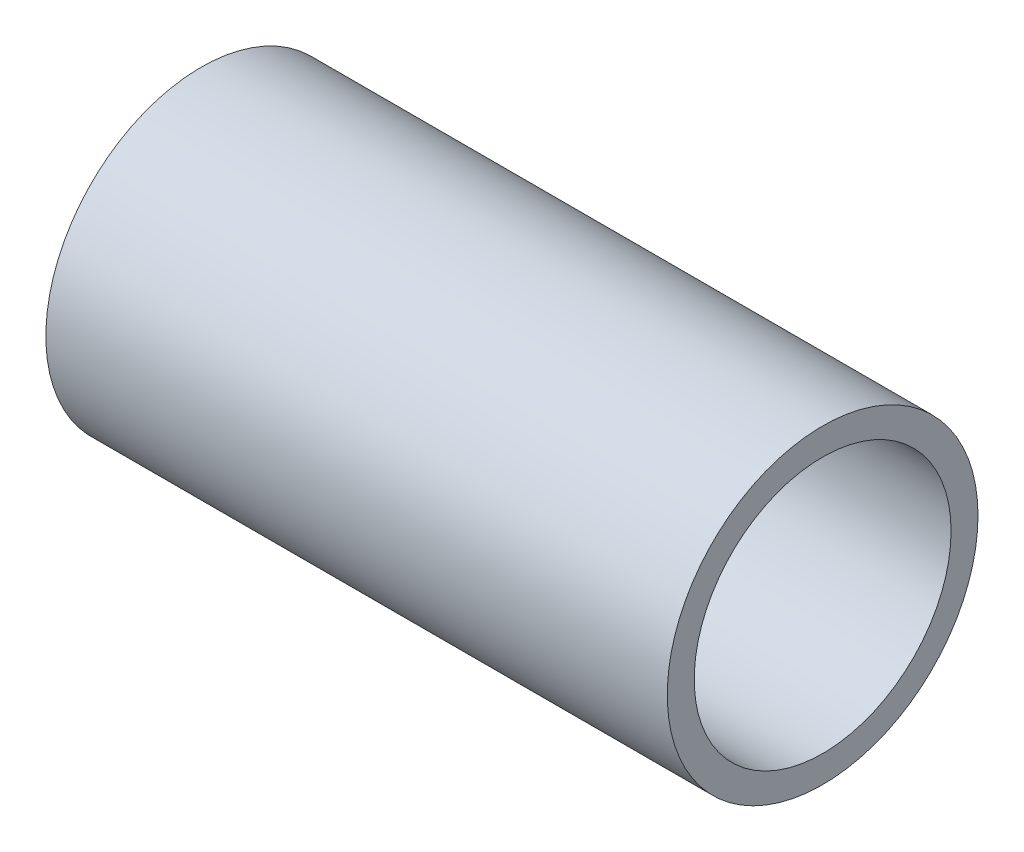
SolidWorks part; units mm, degrees
material "6061 Alloy"
ref_plane "Front Plane" through (0, 0, 0) normal (0, 0, 1) x (1, 0, 0)
ref_plane "Top Plane" through (0, 0, 0) normal (0, 1, 0) x (1, 0, 0)
ref_plane "Right Plane" through (0, 0, 0) normal (1, 0, 0) x (0, 0, -1)
sketch "Sketch1" plane through (0, 0, 0) normal (1, 0, 0) x (0, 0, -1)
  circle A0 centre (0, 0) radius 9.525
  circle A1 centre (0, 0) radius 7.874
  dimension "D1" = 19.05
  dimension "D2" = 15.748
extrude "Boss-Extrude1" add sketch "Sketch1" along normal mid plane 38.1
